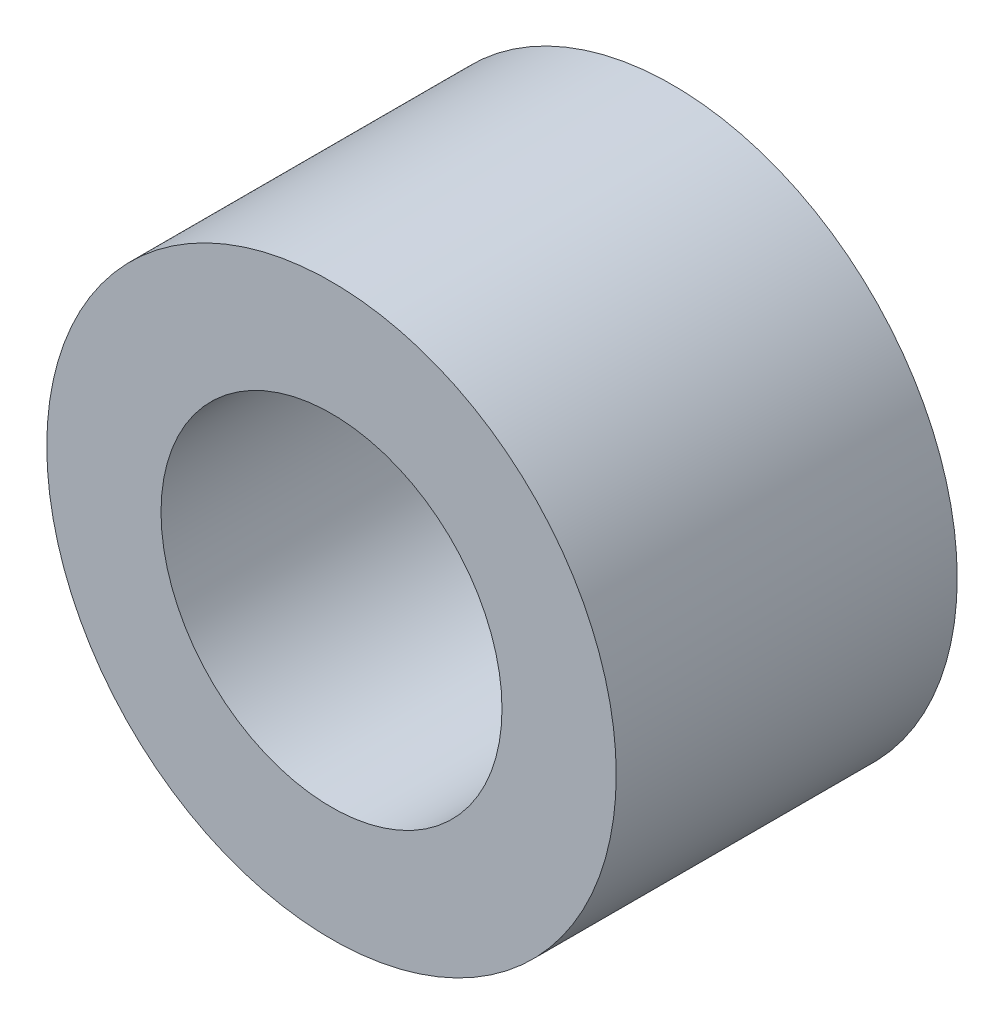
SolidWorks part; units mm, degrees
ref_plane "Front Plane" through (0, 0, 0) normal (0, 0, 1) x (1, 0, 0)
ref_plane "Top Plane" through (0, 0, 0) normal (0, 1, 0) x (1, 0, 0)
ref_plane "Right Plane" through (0, 0, 0) normal (1, 0, 0) x (0, 0, -1)
sketch "Sketch1" plane through (0, 0, 0) normal (0, 0, 1) x (1, 0, 0)
  circle A0 centre (0, 0) radius 5.01
  circle A1 centre (0, 0) radius 3
  dimension "D1" = 10.02
  dimension "ID" = 6
extrude "Extrude1" add sketch "Sketch1" along normal mid plane 6
sketch "Sketch2" plane through (0, 0, 0) normal (1, 0, 0) x (0, 0, -1)
  line L0 (-3, -3) -> (3, -3) construction
  line L3 (3, 3) -> (-3, 3) construction
  line L5 (-3, -3) -> (3, -3)
  line L6 (3, 3) -> (-3, 3)
sketch "Sketch4" plane through (0, 0, 3) normal (0, 0, 1) x (1, 0, 0)
  line L0 (0, 0) -> (-2.1213, 2.1213)
  line L1 (0, -5.5) -> (0, 5.5) construction
  circle A0 centre (0, 0) radius 3 construction
  dimension "D1" = 45
